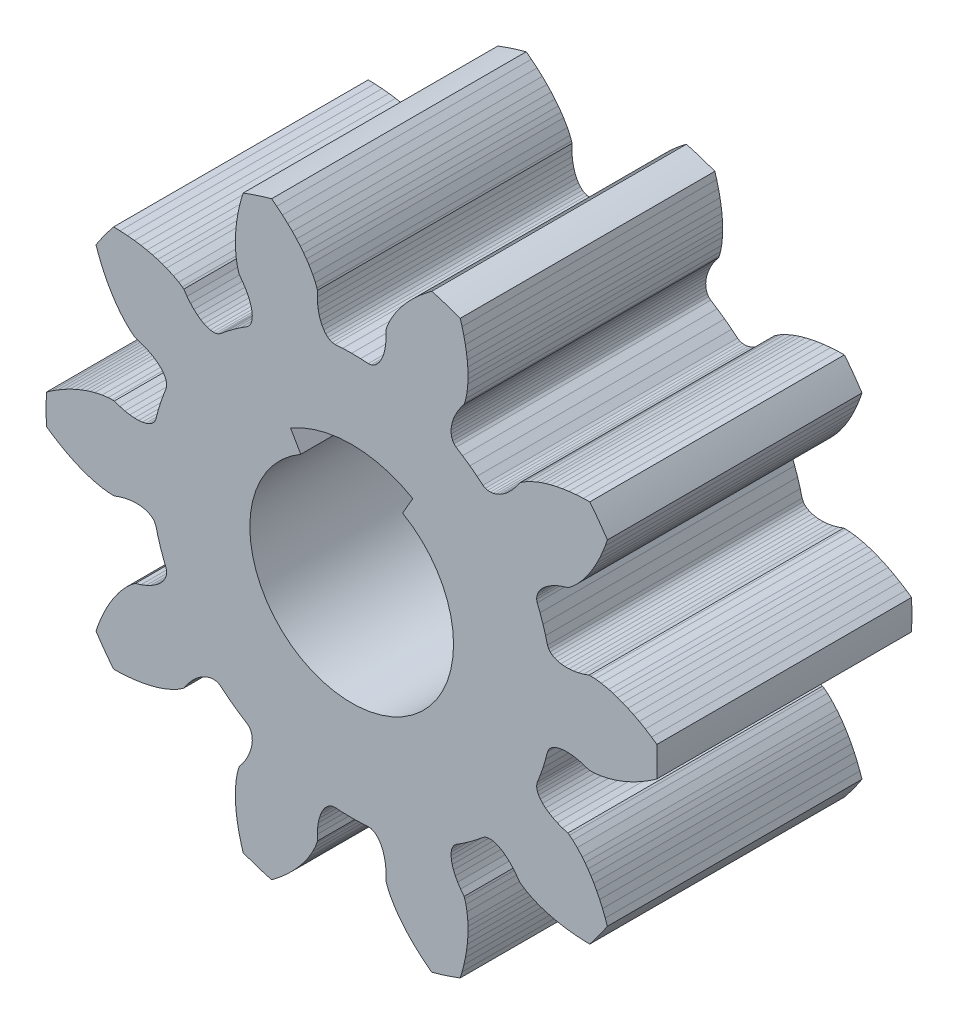
SolidWorks part; units mm, degrees
ref_plane "Front Plane" through (0, 0, 0) normal (0, 0, 1) x (1, 0, 0)
ref_plane "Top Plane" through (0, 0, 0) normal (0, 1, 0) x (1, 0, 0)
ref_plane "Right Plane" through (0, 0, 0) normal (1, 0, 0) x (0, 0, -1)
sketch "Model" plane through (0, 0, 0) normal (0, 0, 1) x (1, 0, 0)
  line L0 (4.9788, 3.1648) -> (4.9257, 3.0301)
  line L1 (4.9257, 3.0301) -> (4.8698, 2.9042)
  line L2 (4.8698, 2.9042) -> (4.8126, 2.7886)
  line L3 (4.8126, 2.7886) -> (4.7546, 2.6829)
  line L4 (4.7546, 2.6829) -> (4.6968, 2.5873)
  line L5 (4.6968, 2.5873) -> (4.6385, 2.4992)
  line L6 (4.6385, 2.4992) -> (4.5835, 2.4234)
  line L7 (4.5835, 2.4234) -> (4.5279, 2.3531)
  line L8 (4.5279, 2.3531) -> (4.429, 2.2427)
  line L9 (4.429, 2.2427) -> (4.3426, 2.161)
  line L10 (4.3426, 2.161) -> (4.2761, 2.108)
  line L11 (4.2761, 2.108) -> (4.245, 2.0868)
  line L12 (4.245, 2.0868) -> (4.1364, 2.054)
  line L13 (4.1364, 2.054) -> (4.038, 2.0161)
  line L14 (4.038, 2.0161) -> (3.95, 1.974)
  line L15 (3.95, 1.974) -> (3.8726, 1.9284)
  line L16 (3.8726, 1.9284) -> (3.806, 1.8802)
  line L17 (3.806, 1.8802) -> (3.7502, 1.8302)
  line L18 (3.7502, 1.8302) -> (3.7052, 1.7791)
  line L19 (3.7052, 1.7791) -> (3.671, 1.7278)
  line L20 (3.671, 1.7278) -> (3.6475, 1.6772)
  line L21 (3.6475, 1.6772) -> (3.6346, 1.6279)
  line L22 (3.6346, 1.6279) -> (3.6321, 1.5809)
  line L23 (3.6321, 1.5809) -> (3.6433, 1.5265)
  line L24 (3.6433, 1.5265) -> (3.6986, 1.3867)
  line L25 (3.6986, 1.3867) -> (3.7567, 1.2206)
  line L26 (3.7567, 1.2206) -> (3.8073, 1.0521)
  line L27 (3.8073, 1.0521) -> (3.8447, 0.9066)
  line L28 (3.8447, 0.9066) -> (3.8677, 0.8559)
  line L29 (3.8677, 0.8559) -> (3.8973, 0.8193)
  line L30 (3.8973, 0.8193) -> (3.9367, 0.7871)
  line L31 (3.9367, 0.7871) -> (3.9855, 0.7599)
  line L32 (3.9855, 0.7599) -> (4.0433, 0.7385)
  line L33 (4.0433, 0.7385) -> (4.1097, 0.7237)
  line L34 (4.1097, 0.7237) -> (4.1843, 0.716)
  line L35 (4.1843, 0.716) -> (4.2665, 0.7161)
  line L36 (4.2665, 0.7161) -> (4.3559, 0.7247)
  line L37 (4.3559, 0.7247) -> (4.4518, 0.7424)
  line L38 (4.4518, 0.7424) -> (4.5537, 0.7696)
  line L39 (4.5537, 0.7696) -> (4.6609, 0.8069)
  line L40 (4.6609, 0.8069) -> (4.6985, 0.8081)
  line L41 (4.6985, 0.8081) -> (4.7834, 0.8042)
  line L42 (4.7834, 0.8042) -> (4.9014, 0.789)
  line L43 (4.9014, 0.789) -> (5.0463, 0.7578)
  line L44 (5.0463, 0.7578) -> (5.1325, 0.7336)
  line L45 (5.1325, 0.7336) -> (5.2216, 0.7045)
  line L46 (5.2216, 0.7045) -> (5.3206, 0.6676)
  line L47 (5.3206, 0.6676) -> (5.4235, 0.6242)
  line L48 (5.4235, 0.6242) -> (5.5326, 0.5727)
  line L49 (5.5326, 0.5727) -> (5.6468, 0.5129)
  line L50 (5.6468, 0.5129) -> (5.766, 0.4438)
  line L51 (5.766, 0.4438) -> (5.8882, 0.3661)
  line L52 (5.8882, 0.3661) -> (5.9928, 0.2936)
  line L53 (5.9928, -0.2936) -> (5.8882, -0.3661)
  line L54 (5.8882, -0.3661) -> (5.766, -0.4438)
  line L55 (5.766, -0.4438) -> (5.6468, -0.5129)
  line L56 (5.6468, -0.5129) -> (5.5326, -0.5727)
  line L57 (5.5326, -0.5727) -> (5.4235, -0.6242)
  line L58 (5.4235, -0.6242) -> (5.3206, -0.6676)
  line L59 (5.3206, -0.6676) -> (5.2216, -0.7045)
  line L60 (5.2216, -0.7045) -> (5.1325, -0.7336)
  line L61 (5.1325, -0.7336) -> (5.0463, -0.7578)
  line L62 (5.0463, -0.7578) -> (4.9014, -0.789)
  line L63 (4.9014, -0.789) -> (4.7834, -0.8042)
  line L64 (4.7834, -0.8042) -> (4.6985, -0.8081)
  line L65 (4.6985, -0.8081) -> (4.6609, -0.8069)
  line L66 (4.6609, -0.8069) -> (4.5537, -0.7696)
  line L67 (4.5537, -0.7696) -> (4.4518, -0.7424)
  line L68 (4.4518, -0.7424) -> (4.3559, -0.7247)
  line L69 (4.3559, -0.7247) -> (4.2665, -0.7161)
  line L70 (4.2665, -0.7161) -> (4.1843, -0.716)
  line L71 (4.1843, -0.716) -> (4.1097, -0.7237)
  line L72 (4.1097, -0.7237) -> (4.0433, -0.7385)
  line L73 (4.0433, -0.7385) -> (3.9855, -0.7599)
  line L74 (3.9855, -0.7599) -> (3.9367, -0.7871)
  line L75 (3.9367, -0.7871) -> (3.8973, -0.8193)
  line L76 (3.8973, -0.8193) -> (3.8677, -0.8559)
  line L77 (3.8677, -0.8559) -> (3.8447, -0.9066)
  line L78 (3.8447, -0.9066) -> (3.8073, -1.0521)
  line L79 (3.8073, -1.0521) -> (3.7567, -1.2206)
  line L80 (3.7567, -1.2206) -> (3.6986, -1.3867)
  line L81 (3.6986, -1.3867) -> (3.6433, -1.5265)
  line L82 (3.6433, -1.5265) -> (3.6321, -1.5809)
  line L83 (3.6321, -1.5809) -> (3.6346, -1.6279)
  line L84 (3.6346, -1.6279) -> (3.6475, -1.6772)
  line L85 (3.6475, -1.6772) -> (3.671, -1.7278)
  line L86 (3.671, -1.7278) -> (3.7052, -1.7791)
  line L87 (3.7052, -1.7791) -> (3.7502, -1.8302)
  line L88 (3.7502, -1.8302) -> (3.806, -1.8802)
  line L89 (3.806, -1.8802) -> (3.8726, -1.9284)
  line L90 (3.8726, -1.9284) -> (3.95, -1.974)
  line L91 (3.95, -1.974) -> (4.038, -2.0161)
  line L92 (4.038, -2.0161) -> (4.1364, -2.054)
  line L93 (4.1364, -2.054) -> (4.245, -2.0868)
  line L94 (4.245, -2.0868) -> (4.2761, -2.108)
  line L95 (4.2761, -2.108) -> (4.3426, -2.161)
  line L96 (4.3426, -2.161) -> (4.429, -2.2427)
  line L97 (4.429, -2.2427) -> (4.5279, -2.3531)
  line L98 (4.5279, -2.3531) -> (4.5835, -2.4234)
  line L99 (4.5835, -2.4234) -> (4.6385, -2.4992)
  line L100 (4.6385, -2.4992) -> (4.6968, -2.5873)
  line L101 (4.6968, -2.5873) -> (4.7546, -2.6829)
  line L102 (4.7546, -2.6829) -> (4.8126, -2.7886)
  line L103 (4.8126, -2.7886) -> (4.8698, -2.9042)
  line L104 (4.8698, -2.9042) -> (4.9257, -3.0301)
  line L105 (4.9257, -3.0301) -> (4.9788, -3.1648)
  line L106 (4.9788, -3.1648) -> (5.0208, -3.285)
  line L107 (4.6757, -3.76) -> (4.5485, -3.7572)
  line L108 (4.5485, -3.7572) -> (4.404, -3.7482)
  line L109 (4.404, -3.7482) -> (4.2669, -3.734)
  line L110 (4.2669, -3.734) -> (4.1393, -3.7153)
  line L111 (4.1393, -3.7153) -> (4.0209, -3.6928)
  line L112 (4.0209, -3.6928) -> (3.9121, -3.6675)
  line L113 (3.9121, -3.6675) -> (3.8103, -3.6392)
  line L114 (3.8103, -3.6392) -> (3.7211, -3.6103)
  line L115 (3.7211, -3.6103) -> (3.6371, -3.5792)
  line L116 (3.6371, -3.5792) -> (3.5016, -3.5192)
  line L117 (3.5016, -3.5192) -> (3.3971, -3.4623)
  line L118 (3.3971, -3.4623) -> (3.3262, -3.4154)
  line L119 (3.3262, -3.4154) -> (3.2964, -3.3924)
  line L120 (3.2964, -3.3924) -> (3.2317, -3.2992)
  line L121 (3.2317, -3.2992) -> (3.1653, -3.2173)
  line L122 (3.1653, -3.2173) -> (3.098, -3.1467)
  line L123 (3.098, -3.1467) -> (3.0308, -3.0872)
  line L124 (3.0308, -3.0872) -> (2.9643, -3.0387)
  line L125 (2.9643, -3.0387) -> (2.8995, -3.0011)
  line L126 (2.8995, -3.0011) -> (2.837, -2.9741)
  line L127 (2.837, -2.9741) -> (2.7777, -2.9574)
  line L128 (2.7777, -2.9574) -> (2.7222, -2.9507)
  line L129 (2.7222, -2.9507) -> (2.6714, -2.9536)
  line L130 (2.6714, -2.9536) -> (2.6259, -2.9658)
  line L131 (2.6259, -2.9658) -> (2.5776, -2.9933)
  line L132 (2.5776, -2.9933) -> (2.4617, -3.0891)
  line L133 (2.4617, -3.0891) -> (2.3218, -3.1956)
  line L134 (2.3218, -3.1956) -> (2.1772, -3.2958)
  line L135 (2.1772, -3.2958) -> (2.0503, -3.3764)
  line L136 (2.0503, -3.3764) -> (2.0092, -3.4139)
  line L137 (2.0092, -3.4139) -> (1.9836, -3.4534)
  line L138 (1.9836, -3.4534) -> (1.9651, -3.5008)
  line L139 (1.9651, -3.5008) -> (1.9543, -3.5556)
  line L140 (1.9543, -3.5556) -> (1.9518, -3.6172)
  line L141 (1.9518, -3.6172) -> (1.9582, -3.6849)
  line L142 (1.9582, -3.6849) -> (1.974, -3.7583)
  line L143 (1.974, -3.7583) -> (1.9995, -3.8364)
  line L144 (1.9995, -3.8364) -> (2.0353, -3.9188)
  line L145 (2.0353, -3.9188) -> (2.0817, -4.0046)
  line L146 (2.0817, -4.0046) -> (2.1391, -4.093)
  line L147 (2.1391, -4.093) -> (2.2077, -4.1834)
  line L148 (2.2077, -4.1834) -> (2.2204, -4.2188)
  line L149 (2.2204, -4.2188) -> (2.243, -4.3008)
  line L150 (2.243, -4.3008) -> (2.2649, -4.4177)
  line L151 (2.2649, -4.4177) -> (2.2801, -4.5651)
  line L152 (2.2801, -4.5651) -> (2.2837, -4.6546)
  line L153 (2.2837, -4.6546) -> (2.2836, -4.7483)
  line L154 (2.2836, -4.7483) -> (2.2791, -4.8539)
  line L155 (2.2791, -4.8539) -> (2.2696, -4.9652)
  line L156 (2.2696, -4.9652) -> (2.2543, -5.0848)
  line L157 (2.2543, -5.0848) -> (2.2327, -5.2119)
  line L158 (2.2327, -5.2119) -> (2.2039, -5.3467)
  line L159 (2.2039, -5.3467) -> (2.1677, -5.4869)
  line L160 (2.1677, -5.4869) -> (2.1311, -5.6087)
  line L161 (1.5727, -5.7902) -> (1.4714, -5.7131)
  line L162 (1.4714, -5.7131) -> (1.3597, -5.621)
  line L163 (1.3597, -5.621) -> (1.2572, -5.5289)
  line L164 (1.2572, -5.5289) -> (1.165, -5.4388)
  line L165 (1.165, -5.4388) -> (1.0823, -5.351)
  line L166 (1.0823, -5.351) -> (1.0092, -5.2665)
  line L167 (1.0092, -5.2665) -> (0.9435, -5.1838)
  line L168 (0.9435, -5.1838) -> (0.8884, -5.108)
  line L169 (0.8884, -5.108) -> (0.8387, -5.0335)
  line L170 (0.8387, -5.0335) -> (0.7643, -4.9053)
  line L171 (0.7643, -4.9053) -> (0.7133, -4.7978)
  line L172 (0.7133, -4.7978) -> (0.6834, -4.7182)
  line L173 (0.6834, -4.7182) -> (0.6728, -4.6821)
  line L174 (0.6728, -4.6821) -> (0.6752, -4.5686)
  line L175 (0.6752, -4.5686) -> (0.6697, -4.4634)
  line L176 (0.6697, -4.4634) -> (0.6568, -4.3667)
  line L177 (0.6568, -4.3667) -> (0.6373, -4.279)
  line L178 (0.6373, -4.279) -> (0.6121, -4.2008)
  line L179 (0.6121, -4.2008) -> (0.5817, -4.1322)
  line L180 (0.5817, -4.1322) -> (0.5471, -4.0736)
  line L181 (0.5471, -4.0736) -> (0.5089, -4.0252)
  line L182 (0.5089, -4.0252) -> (0.4679, -3.9873)
  line L183 (0.4679, -3.9873) -> (0.4251, -3.9598)
  line L184 (0.4251, -3.9598) -> (0.3812, -3.9429)
  line L185 (0.3812, -3.9429) -> (0.3259, -3.9367)
  line L186 (0.3259, -3.9367) -> (0.1759, -3.9461)
  line L187 (0.1759, -3.9461) -> (0, -3.95)
  line L188 (0, -3.95) -> (-0.1759, -3.9461)
  line L189 (-0.1759, -3.9461) -> (-0.3259, -3.9367)
  line L190 (-0.3259, -3.9367) -> (-0.3812, -3.9429)
  line L191 (-0.3812, -3.9429) -> (-0.4251, -3.9598)
  line L192 (-0.4251, -3.9598) -> (-0.4679, -3.9873)
  line L193 (-0.4679, -3.9873) -> (-0.5089, -4.0252)
  line L194 (-0.5089, -4.0252) -> (-0.5471, -4.0736)
  line L195 (-0.5471, -4.0736) -> (-0.5817, -4.1322)
  line L196 (-0.5817, -4.1322) -> (-0.6121, -4.2008)
  line L197 (-0.6121, -4.2008) -> (-0.6373, -4.279)
  line L198 (-0.6373, -4.279) -> (-0.6568, -4.3667)
  line L199 (-0.6568, -4.3667) -> (-0.6697, -4.4634)
  line L200 (-0.6697, -4.4634) -> (-0.6752, -4.5686)
  line L201 (-0.6752, -4.5686) -> (-0.6728, -4.6821)
  line L202 (-0.6728, -4.6821) -> (-0.6834, -4.7182)
  line L203 (-0.6834, -4.7182) -> (-0.7133, -4.7978)
  line L204 (-0.7133, -4.7978) -> (-0.7643, -4.9053)
  line L205 (-0.7643, -4.9053) -> (-0.8387, -5.0335)
  line L206 (-0.8387, -5.0335) -> (-0.8884, -5.108)
  line L207 (-0.8884, -5.108) -> (-0.9435, -5.1838)
  line L208 (-0.9435, -5.1838) -> (-1.0092, -5.2665)
  line L209 (-1.0092, -5.2665) -> (-1.0823, -5.351)
  line L210 (-1.0823, -5.351) -> (-1.165, -5.4388)
  line L211 (-1.165, -5.4388) -> (-1.2572, -5.5289)
  line L212 (-1.2572, -5.5289) -> (-1.3597, -5.621)
  line L213 (-1.3597, -5.621) -> (-1.4714, -5.7131)
  line L214 (-1.4714, -5.7131) -> (-1.5727, -5.7902)
  line L215 (-2.1311, -5.6087) -> (-2.1677, -5.4869)
  line L216 (-2.1677, -5.4869) -> (-2.2039, -5.3467)
  line L217 (-2.2039, -5.3467) -> (-2.2327, -5.2119)
  line L218 (-2.2327, -5.2119) -> (-2.2543, -5.0848)
  line L219 (-2.2543, -5.0848) -> (-2.2696, -4.9652)
  line L220 (-2.2696, -4.9652) -> (-2.2791, -4.8539)
  line L221 (-2.2791, -4.8539) -> (-2.2836, -4.7483)
  line L222 (-2.2836, -4.7483) -> (-2.2837, -4.6546)
  line L223 (-2.2837, -4.6546) -> (-2.2801, -4.5651)
  line L224 (-2.2801, -4.5651) -> (-2.2649, -4.4177)
  line L225 (-2.2649, -4.4177) -> (-2.243, -4.3008)
  line L226 (-2.243, -4.3008) -> (-2.2204, -4.2188)
  line L227 (-2.2204, -4.2188) -> (-2.2077, -4.1834)
  line L228 (-2.2077, -4.1834) -> (-2.1391, -4.093)
  line L229 (-2.1391, -4.093) -> (-2.0817, -4.0046)
  line L230 (-2.0817, -4.0046) -> (-2.0353, -3.9188)
  line L231 (-2.0353, -3.9188) -> (-1.9995, -3.8364)
  line L232 (-1.9995, -3.8364) -> (-1.974, -3.7583)
  line L233 (-1.974, -3.7583) -> (-1.9582, -3.6849)
  line L234 (-1.9582, -3.6849) -> (-1.9518, -3.6172)
  line L235 (-1.9518, -3.6172) -> (-1.9543, -3.5556)
  line L236 (-1.9543, -3.5556) -> (-1.9651, -3.5008)
  line L237 (-1.9651, -3.5008) -> (-1.9836, -3.4534)
  line L238 (-1.9836, -3.4534) -> (-2.0092, -3.4139)
  line L239 (-2.0092, -3.4139) -> (-2.0503, -3.3764)
  line L240 (-2.0503, -3.3764) -> (-2.1772, -3.2958)
  line L241 (-2.1772, -3.2958) -> (-2.3218, -3.1956)
  line L242 (-2.3218, -3.1956) -> (-2.4617, -3.0891)
  line L243 (-2.4617, -3.0891) -> (-2.5776, -2.9933)
  line L244 (-2.5776, -2.9933) -> (-2.6259, -2.9658)
  line L245 (-2.6259, -2.9658) -> (-2.6714, -2.9536)
  line L246 (-2.6714, -2.9536) -> (-2.7222, -2.9507)
  line L247 (-2.7222, -2.9507) -> (-2.7777, -2.9574)
  line L248 (-2.7777, -2.9574) -> (-2.837, -2.9741)
  line L249 (-2.837, -2.9741) -> (-2.8995, -3.0011)
  line L250 (-2.8995, -3.0011) -> (-2.9643, -3.0387)
  line L251 (-2.9643, -3.0387) -> (-3.0308, -3.0872)
  line L252 (-3.0308, -3.0872) -> (-3.098, -3.1467)
  line L253 (-3.098, -3.1467) -> (-3.1653, -3.2173)
  line L254 (-3.1653, -3.2173) -> (-3.2317, -3.2992)
  line L255 (-3.2317, -3.2992) -> (-3.2964, -3.3924)
  line L256 (-3.2964, -3.3924) -> (-3.3262, -3.4154)
  line L257 (-3.3262, -3.4154) -> (-3.3971, -3.4623)
  line L258 (-3.3971, -3.4623) -> (-3.5016, -3.5192)
  line L259 (-3.5016, -3.5192) -> (-3.6371, -3.5792)
  line L260 (-3.6371, -3.5792) -> (-3.7211, -3.6103)
  line L261 (-3.7211, -3.6103) -> (-3.8103, -3.6392)
  line L262 (-3.8103, -3.6392) -> (-3.9121, -3.6675)
  line L263 (-3.9121, -3.6675) -> (-4.0209, -3.6928)
  line L264 (-4.0209, -3.6928) -> (-4.1393, -3.7153)
  line L265 (-4.1393, -3.7153) -> (-4.2669, -3.734)
  line L266 (-4.2669, -3.734) -> (-4.404, -3.7482)
  line L267 (-4.404, -3.7482) -> (-4.5485, -3.7572)
  line L268 (-4.5485, -3.7572) -> (-4.6757, -3.76)
  line L269 (-5.0208, -3.285) -> (-4.9788, -3.1648)
  line L270 (-4.9788, -3.1648) -> (-4.9257, -3.0301)
  line L271 (-4.9257, -3.0301) -> (-4.8698, -2.9042)
  line L272 (-4.8698, -2.9042) -> (-4.8126, -2.7886)
  line L273 (-4.8126, -2.7886) -> (-4.7546, -2.6829)
  line L274 (-4.7546, -2.6829) -> (-4.6968, -2.5873)
  line L275 (-4.6968, -2.5873) -> (-4.6385, -2.4992)
  line L276 (-4.6385, -2.4992) -> (-4.5835, -2.4234)
  line L277 (-4.5835, -2.4234) -> (-4.5279, -2.3531)
  line L278 (-4.5279, -2.3531) -> (-4.429, -2.2427)
  line L279 (-4.429, -2.2427) -> (-4.3426, -2.161)
  line L280 (-4.3426, -2.161) -> (-4.2761, -2.108)
  line L281 (-4.2761, -2.108) -> (-4.245, -2.0868)
  line L282 (-4.245, -2.0868) -> (-4.1364, -2.054)
  line L283 (-4.1364, -2.054) -> (-4.038, -2.0161)
  line L284 (-4.038, -2.0161) -> (-3.95, -1.974)
  line L285 (-3.95, -1.974) -> (-3.8726, -1.9284)
  line L286 (-3.8726, -1.9284) -> (-3.806, -1.8802)
  line L287 (-3.806, -1.8802) -> (-3.7502, -1.8302)
  line L288 (-3.7502, -1.8302) -> (-3.7052, -1.7791)
  line L289 (-3.7052, -1.7791) -> (-3.671, -1.7278)
  line L290 (-3.671, -1.7278) -> (-3.6475, -1.6772)
  line L291 (-3.6475, -1.6772) -> (-3.6346, -1.6279)
  line L292 (-3.6346, -1.6279) -> (-3.6321, -1.5809)
  line L293 (-3.6321, -1.5809) -> (-3.6433, -1.5265)
  line L294 (-3.6433, -1.5265) -> (-3.6986, -1.3867)
  line L295 (-3.6986, -1.3867) -> (-3.7567, -1.2206)
  line L296 (-3.7567, -1.2206) -> (-3.8073, -1.0521)
  line L297 (-3.8073, -1.0521) -> (-3.8447, -0.9066)
  line L298 (-3.8447, -0.9066) -> (-3.8677, -0.8559)
  line L299 (-3.8677, -0.8559) -> (-3.8973, -0.8193)
  line L300 (-3.8973, -0.8193) -> (-3.9367, -0.7871)
  line L301 (-3.9367, -0.7871) -> (-3.9855, -0.7599)
  line L302 (-3.9855, -0.7599) -> (-4.0433, -0.7385)
  line L303 (-4.0433, -0.7385) -> (-4.1097, -0.7237)
  line L304 (-4.1097, -0.7237) -> (-4.1843, -0.716)
  line L305 (-4.1843, -0.716) -> (-4.2665, -0.7161)
  line L306 (-4.2665, -0.7161) -> (-4.3559, -0.7247)
  line L307 (-4.3559, -0.7247) -> (-4.4518, -0.7424)
  line L308 (-4.4518, -0.7424) -> (-4.5537, -0.7696)
  line L309 (-4.5537, -0.7696) -> (-4.6609, -0.8069)
  line L310 (-4.6609, -0.8069) -> (-4.6985, -0.8081)
  line L311 (-4.6985, -0.8081) -> (-4.7834, -0.8042)
  line L312 (-4.7834, -0.8042) -> (-4.9014, -0.789)
  line L313 (-4.9014, -0.789) -> (-5.0463, -0.7578)
  line L314 (-5.0463, -0.7578) -> (-5.1325, -0.7336)
  line L315 (-5.1325, -0.7336) -> (-5.2216, -0.7045)
  line L316 (-5.2216, -0.7045) -> (-5.3206, -0.6676)
  line L317 (-5.3206, -0.6676) -> (-5.4235, -0.6242)
  line L318 (-5.4235, -0.6242) -> (-5.5326, -0.5727)
  line L319 (-5.5326, -0.5727) -> (-5.6468, -0.5129)
  line L320 (-5.6468, -0.5129) -> (-5.766, -0.4438)
  line L321 (-5.766, -0.4438) -> (-5.8882, -0.3661)
  line L322 (-5.8882, -0.3661) -> (-5.9928, -0.2936)
  line L323 (-5.9928, 0.2936) -> (-5.8882, 0.3661)
  line L324 (-5.8882, 0.3661) -> (-5.766, 0.4438)
  line L325 (-5.766, 0.4438) -> (-5.6468, 0.5129)
  line L326 (-5.6468, 0.5129) -> (-5.5326, 0.5727)
  line L327 (-5.5326, 0.5727) -> (-5.4235, 0.6242)
  line L328 (-5.4235, 0.6242) -> (-5.3206, 0.6676)
  line L329 (-5.3206, 0.6676) -> (-5.2216, 0.7045)
  line L330 (-5.2216, 0.7045) -> (-5.1325, 0.7336)
  line L331 (-5.1325, 0.7336) -> (-5.0463, 0.7578)
  line L332 (-5.0463, 0.7578) -> (-4.9014, 0.789)
  line L333 (-4.9014, 0.789) -> (-4.7834, 0.8042)
  line L334 (-4.7834, 0.8042) -> (-4.6985, 0.8081)
  line L335 (-4.6985, 0.8081) -> (-4.6609, 0.8069)
  line L336 (-4.6609, 0.8069) -> (-4.5537, 0.7696)
  line L337 (-4.5537, 0.7696) -> (-4.4518, 0.7424)
  line L338 (-4.4518, 0.7424) -> (-4.3559, 0.7247)
  line L339 (-4.3559, 0.7247) -> (-4.2665, 0.7161)
  line L340 (-4.2665, 0.7161) -> (-4.1843, 0.716)
  line L341 (-4.1843, 0.716) -> (-4.1097, 0.7237)
  line L342 (-4.1097, 0.7237) -> (-4.0433, 0.7385)
  line L343 (-4.0433, 0.7385) -> (-3.9855, 0.7599)
  line L344 (-3.9855, 0.7599) -> (-3.9367, 0.7871)
  line L345 (-3.9367, 0.7871) -> (-3.8973, 0.8193)
  line L346 (-3.8973, 0.8193) -> (-3.8677, 0.8559)
  line L347 (-3.8677, 0.8559) -> (-3.8447, 0.9066)
  line L348 (-3.8447, 0.9066) -> (-3.8073, 1.0521)
  line L349 (-3.8073, 1.0521) -> (-3.7567, 1.2206)
  line L350 (-3.7567, 1.2206) -> (-3.6986, 1.3867)
  line L351 (-3.6986, 1.3867) -> (-3.6433, 1.5265)
  line L352 (-3.6433, 1.5265) -> (-3.6321, 1.5809)
  line L353 (-3.6321, 1.5809) -> (-3.6346, 1.6279)
  line L354 (-3.6346, 1.6279) -> (-3.6475, 1.6772)
  line L355 (-3.6475, 1.6772) -> (-3.671, 1.7278)
  line L356 (-3.671, 1.7278) -> (-3.7052, 1.7791)
  line L357 (-3.7052, 1.7791) -> (-3.7502, 1.8302)
  line L358 (-3.7502, 1.8302) -> (-3.806, 1.8802)
  line L359 (-3.806, 1.8802) -> (-3.8726, 1.9284)
  line L360 (-3.8726, 1.9284) -> (-3.95, 1.974)
  line L361 (-3.95, 1.974) -> (-4.038, 2.0161)
  line L362 (-4.038, 2.0161) -> (-4.1364, 2.054)
  line L363 (-4.1364, 2.054) -> (-4.245, 2.0868)
  line L364 (-4.245, 2.0868) -> (-4.2761, 2.108)
  line L365 (-4.2761, 2.108) -> (-4.3426, 2.161)
  line L366 (-4.3426, 2.161) -> (-4.429, 2.2427)
  line L367 (-4.429, 2.2427) -> (-4.5279, 2.3531)
  line L368 (-4.5279, 2.3531) -> (-4.5835, 2.4234)
  line L369 (-4.5835, 2.4234) -> (-4.6385, 2.4992)
  line L370 (-4.6385, 2.4992) -> (-4.6968, 2.5873)
  line L371 (-4.6968, 2.5873) -> (-4.7546, 2.6829)
  line L372 (-4.7546, 2.6829) -> (-4.8126, 2.7886)
  line L373 (-4.8126, 2.7886) -> (-4.8698, 2.9042)
  line L374 (-4.8698, 2.9042) -> (-4.9257, 3.0301)
  line L375 (-4.9257, 3.0301) -> (-4.9788, 3.1648)
  line L376 (-4.9788, 3.1648) -> (-5.0208, 3.285)
  line L377 (-4.6757, 3.76) -> (-4.5485, 3.7572)
  line L378 (-4.5485, 3.7572) -> (-4.404, 3.7482)
  line L379 (-4.404, 3.7482) -> (-4.2669, 3.734)
  line L380 (-4.2669, 3.734) -> (-4.1393, 3.7153)
  line L381 (-4.1393, 3.7153) -> (-4.0209, 3.6928)
  line L382 (-4.0209, 3.6928) -> (-3.9121, 3.6675)
  line L383 (-3.9121, 3.6675) -> (-3.8103, 3.6392)
  line L384 (-3.8103, 3.6392) -> (-3.7211, 3.6103)
  line L385 (-3.7211, 3.6103) -> (-3.6371, 3.5792)
  line L386 (-3.6371, 3.5792) -> (-3.5016, 3.5192)
  line L387 (-3.5016, 3.5192) -> (-3.3971, 3.4623)
  line L388 (-3.3971, 3.4623) -> (-3.3262, 3.4154)
  line L389 (-3.3262, 3.4154) -> (-3.2964, 3.3924)
  line L390 (-3.2964, 3.3924) -> (-3.2317, 3.2992)
  line L391 (-3.2317, 3.2992) -> (-3.1653, 3.2173)
  line L392 (-3.1653, 3.2173) -> (-3.098, 3.1467)
  line L393 (-3.098, 3.1467) -> (-3.0308, 3.0872)
  line L394 (-3.0308, 3.0872) -> (-2.9643, 3.0387)
  line L395 (-2.9643, 3.0387) -> (-2.8995, 3.0011)
  line L396 (-2.8995, 3.0011) -> (-2.837, 2.9741)
  line L397 (-2.837, 2.9741) -> (-2.7777, 2.9574)
  line L398 (-2.7777, 2.9574) -> (-2.7222, 2.9507)
  line L399 (-2.7222, 2.9507) -> (-2.6714, 2.9536)
  line L400 (-2.6714, 2.9536) -> (-2.6259, 2.9658)
  line L401 (-2.6259, 2.9658) -> (-2.5776, 2.9933)
  line L402 (-2.5776, 2.9933) -> (-2.4617, 3.0891)
  line L403 (-2.4617, 3.0891) -> (-2.3218, 3.1956)
  line L404 (-2.3218, 3.1956) -> (-2.1772, 3.2958)
  line L405 (-2.1772, 3.2958) -> (-2.0503, 3.3764)
  line L406 (-2.0503, 3.3764) -> (-2.0092, 3.4139)
  line L407 (-2.0092, 3.4139) -> (-1.9836, 3.4534)
  line L408 (-1.9836, 3.4534) -> (-1.9651, 3.5008)
  line L409 (-1.9651, 3.5008) -> (-1.9543, 3.5556)
  line L410 (-1.9543, 3.5556) -> (-1.9518, 3.6172)
  line L411 (-1.9518, 3.6172) -> (-1.9582, 3.6849)
  line L412 (-1.9582, 3.6849) -> (-1.974, 3.7583)
  line L413 (-1.974, 3.7583) -> (-1.9995, 3.8364)
  line L414 (-1.9995, 3.8364) -> (-2.0353, 3.9188)
  line L415 (-2.0353, 3.9188) -> (-2.0817, 4.0046)
  line L416 (-2.0817, 4.0046) -> (-2.1391, 4.093)
  line L417 (-2.1391, 4.093) -> (-2.2077, 4.1834)
  line L418 (-2.2077, 4.1834) -> (-2.2204, 4.2188)
  line L419 (-2.2204, 4.2188) -> (-2.243, 4.3008)
  line L420 (-2.243, 4.3008) -> (-2.2649, 4.4177)
  line L421 (-2.2649, 4.4177) -> (-2.2801, 4.5651)
  line L422 (-2.2801, 4.5651) -> (-2.2837, 4.6546)
  line L423 (-2.2837, 4.6546) -> (-2.2836, 4.7483)
  line L424 (-2.2836, 4.7483) -> (-2.2791, 4.8539)
  line L425 (-2.2791, 4.8539) -> (-2.2696, 4.9652)
  line L426 (-2.2696, 4.9652) -> (-2.2543, 5.0848)
  line L427 (-2.2543, 5.0848) -> (-2.2327, 5.2119)
  line L428 (-2.2327, 5.2119) -> (-2.2039, 5.3467)
  line L429 (-2.2039, 5.3467) -> (-2.1677, 5.4869)
  line L430 (-2.1677, 5.4869) -> (-2.1311, 5.6087)
  line L431 (-1.5727, 5.7902) -> (-1.4714, 5.7131)
  line L432 (-1.4714, 5.7131) -> (-1.3597, 5.621)
  line L433 (-1.3597, 5.621) -> (-1.2572, 5.5289)
  line L434 (-1.2572, 5.5289) -> (-1.165, 5.4388)
  line L435 (-1.165, 5.4388) -> (-1.0823, 5.351)
  line L436 (-1.0823, 5.351) -> (-1.0092, 5.2665)
  line L437 (-1.0092, 5.2665) -> (-0.9435, 5.1838)
  line L438 (-0.9435, 5.1838) -> (-0.8884, 5.108)
  line L439 (-0.8884, 5.108) -> (-0.8387, 5.0335)
  line L440 (-0.8387, 5.0335) -> (-0.7643, 4.9053)
  line L441 (-0.7643, 4.9053) -> (-0.7133, 4.7978)
  line L442 (-0.7133, 4.7978) -> (-0.6834, 4.7182)
  line L443 (-0.6834, 4.7182) -> (-0.6728, 4.6821)
  line L444 (-0.6728, 4.6821) -> (-0.6752, 4.5686)
  line L445 (-0.6752, 4.5686) -> (-0.6697, 4.4634)
  line L446 (-0.6697, 4.4634) -> (-0.6568, 4.3667)
  line L447 (-0.6568, 4.3667) -> (-0.6373, 4.279)
  line L448 (-0.6373, 4.279) -> (-0.6121, 4.2008)
  line L449 (-0.6121, 4.2008) -> (-0.5817, 4.1322)
  line L450 (-0.5817, 4.1322) -> (-0.5471, 4.0736)
  line L451 (-0.5471, 4.0736) -> (-0.5089, 4.0252)
  line L452 (-0.5089, 4.0252) -> (-0.4679, 3.9873)
  line L453 (-0.4679, 3.9873) -> (-0.4251, 3.9598)
  line L454 (-0.4251, 3.9598) -> (-0.3812, 3.9429)
  line L455 (-0.3812, 3.9429) -> (-0.3259, 3.9367)
  line L456 (-0.3259, 3.9367) -> (-0.1759, 3.9461)
  line L457 (-0.1759, 3.9461) -> (0, 3.95)
  line L458 (0, 3.95) -> (0.1759, 3.9461)
  line L459 (0.1759, 3.9461) -> (0.3259, 3.9367)
  line L460 (0.3259, 3.9367) -> (0.3812, 3.9429)
  line L461 (0.3812, 3.9429) -> (0.4251, 3.9598)
  line L462 (0.4251, 3.9598) -> (0.4679, 3.9873)
  line L463 (0.4679, 3.9873) -> (0.5089, 4.0252)
  line L464 (0.5089, 4.0252) -> (0.5471, 4.0736)
  line L465 (0.5471, 4.0736) -> (0.5817, 4.1322)
  line L466 (0.5817, 4.1322) -> (0.6121, 4.2008)
  line L467 (0.6121, 4.2008) -> (0.6373, 4.279)
  line L468 (0.6373, 4.279) -> (0.6568, 4.3667)
  line L469 (0.6568, 4.3667) -> (0.6697, 4.4634)
  line L470 (0.6697, 4.4634) -> (0.6752, 4.5686)
  line L471 (0.6752, 4.5686) -> (0.6728, 4.6821)
  line L472 (0.6728, 4.6821) -> (0.6834, 4.7182)
  line L473 (0.6834, 4.7182) -> (0.7133, 4.7978)
  line L474 (0.7133, 4.7978) -> (0.7643, 4.9053)
  line L475 (0.7643, 4.9053) -> (0.8387, 5.0335)
  line L476 (0.8387, 5.0335) -> (0.8884, 5.108)
  line L477 (0.8884, 5.108) -> (0.9435, 5.1838)
  line L478 (0.9435, 5.1838) -> (1.0092, 5.2665)
  line L479 (1.0092, 5.2665) -> (1.0823, 5.351)
  line L480 (1.0823, 5.351) -> (1.165, 5.4388)
  line L481 (1.165, 5.4388) -> (1.2572, 5.5289)
  line L482 (1.2572, 5.5289) -> (1.3597, 5.621)
  line L483 (1.3597, 5.621) -> (1.4714, 5.7131)
  line L484 (1.4714, 5.7131) -> (1.5727, 5.7902)
  line L485 (2.1311, 5.6087) -> (2.1677, 5.4869)
  line L486 (2.1677, 5.4869) -> (2.2039, 5.3467)
  line L487 (2.2039, 5.3467) -> (2.2327, 5.2119)
  line L488 (2.2327, 5.2119) -> (2.2543, 5.0848)
  line L489 (2.2543, 5.0848) -> (2.2696, 4.9652)
  line L490 (2.2696, 4.9652) -> (2.2791, 4.8539)
  line L491 (2.2791, 4.8539) -> (2.2836, 4.7483)
  line L492 (2.2836, 4.7483) -> (2.2837, 4.6546)
  line L493 (2.2837, 4.6546) -> (2.2801, 4.5651)
  line L494 (2.2801, 4.5651) -> (2.2649, 4.4177)
  line L495 (2.2649, 4.4177) -> (2.243, 4.3008)
  line L496 (2.243, 4.3008) -> (2.2204, 4.2188)
  line L497 (2.2204, 4.2188) -> (2.2077, 4.1834)
  line L498 (2.2077, 4.1834) -> (2.1391, 4.093)
  line L499 (2.1391, 4.093) -> (2.0817, 4.0046)
  line L500 (2.0817, 4.0046) -> (2.0353, 3.9188)
  line L501 (2.0353, 3.9188) -> (1.9995, 3.8364)
  line L502 (1.9995, 3.8364) -> (1.974, 3.7583)
  line L503 (1.974, 3.7583) -> (1.9582, 3.6849)
  line L504 (1.9582, 3.6849) -> (1.9518, 3.6172)
  line L505 (1.9518, 3.6172) -> (1.9543, 3.5556)
  line L506 (1.9543, 3.5556) -> (1.9651, 3.5008)
  line L507 (1.9651, 3.5008) -> (1.9836, 3.4534)
  line L508 (1.9836, 3.4534) -> (2.0092, 3.4139)
  line L509 (2.0092, 3.4139) -> (2.0503, 3.3764)
  line L510 (2.0503, 3.3764) -> (2.1772, 3.2958)
  line L511 (2.1772, 3.2958) -> (2.3218, 3.1956)
  line L512 (2.3218, 3.1956) -> (2.4617, 3.0891)
  line L513 (2.4617, 3.0891) -> (2.5776, 2.9933)
  line L514 (2.5776, 2.9933) -> (2.6259, 2.9658)
  line L515 (2.6259, 2.9658) -> (2.6714, 2.9536)
  line L516 (2.6714, 2.9536) -> (2.7222, 2.9507)
  line L517 (2.7222, 2.9507) -> (2.7777, 2.9574)
  line L518 (2.7777, 2.9574) -> (2.837, 2.9741)
  line L519 (2.837, 2.9741) -> (2.8995, 3.0011)
  line L520 (2.8995, 3.0011) -> (2.9643, 3.0387)
  line L521 (2.9643, 3.0387) -> (3.0308, 3.0872)
  line L522 (3.0308, 3.0872) -> (3.098, 3.1467)
  line L523 (3.098, 3.1467) -> (3.1653, 3.2173)
  line L524 (3.1653, 3.2173) -> (3.2317, 3.2992)
  line L525 (3.2317, 3.2992) -> (3.2964, 3.3924)
  line L526 (3.2964, 3.3924) -> (3.3262, 3.4154)
  line L527 (3.3262, 3.4154) -> (3.3971, 3.4623)
  line L528 (3.3971, 3.4623) -> (3.5016, 3.5192)
  line L529 (3.5016, 3.5192) -> (3.6371, 3.5792)
  line L530 (3.6371, 3.5792) -> (3.7211, 3.6103)
  line L531 (3.7211, 3.6103) -> (3.8103, 3.6392)
  line L532 (3.8103, 3.6392) -> (3.9121, 3.6675)
  line L533 (3.9121, 3.6675) -> (4.0209, 3.6928)
  line L534 (4.0209, 3.6928) -> (4.1393, 3.7153)
  line L535 (4.1393, 3.7153) -> (4.2669, 3.734)
  line L536 (4.2669, 3.734) -> (4.404, 3.7482)
  line L537 (4.404, 3.7482) -> (4.5485, 3.7572)
  line L538 (4.5485, 3.7572) -> (4.6757, 3.76)
  line L539 (5.0208, 3.285) -> (4.9788, 3.1648)
  circle A1 centre (0, 0) radius 2
  arc A2 (5.9928, -0.2936) -> (5.9928, 0.2936) centre (0, 0) ccw
  arc A3 (4.6757, -3.76) -> (5.0208, -3.285) centre (0, 0) ccw
  arc A4 (1.5727, -5.7902) -> (2.1311, -5.6087) centre (0, 0) ccw
  arc A5 (-2.1311, -5.6087) -> (-1.5727, -5.7902) centre (0, 0) ccw
  arc A6 (-5.0208, -3.285) -> (-4.6757, -3.76) centre (0, 0) ccw
  arc A7 (-5.9928, 0.2936) -> (-5.9928, -0.2936) centre (0, 0) ccw
  arc A8 (-4.6757, 3.76) -> (-5.0208, 3.285) centre (0, 0) ccw
  arc A9 (-1.5727, 5.7902) -> (-2.1311, 5.6087) centre (0, 0) ccw
  arc A10 (2.1311, 5.6087) -> (1.5727, 5.7902) centre (0, 0) ccw
  arc A11 (5.0208, 3.285) -> (4.6757, 3.76) centre (0, 0) ccw
extrude "Boss-Extrude1" add sketch "Model" along normal blind 5
sketch "Sketch2" plane through (0, 0, 5) normal (0, 0, 1) x (1, 0, 0)
  line L1 (0, 0) -> (-1.2, 2.0785)
  line L2 (0, 0) -> (1.2, 2.0785)
  arc A0 (1.2, 2.0785) -> (-1.2, 2.0785) centre (0, 0) ccw
extrude "Cut-Extrude2" cut sketch "Sketch2" against normal blind 14
